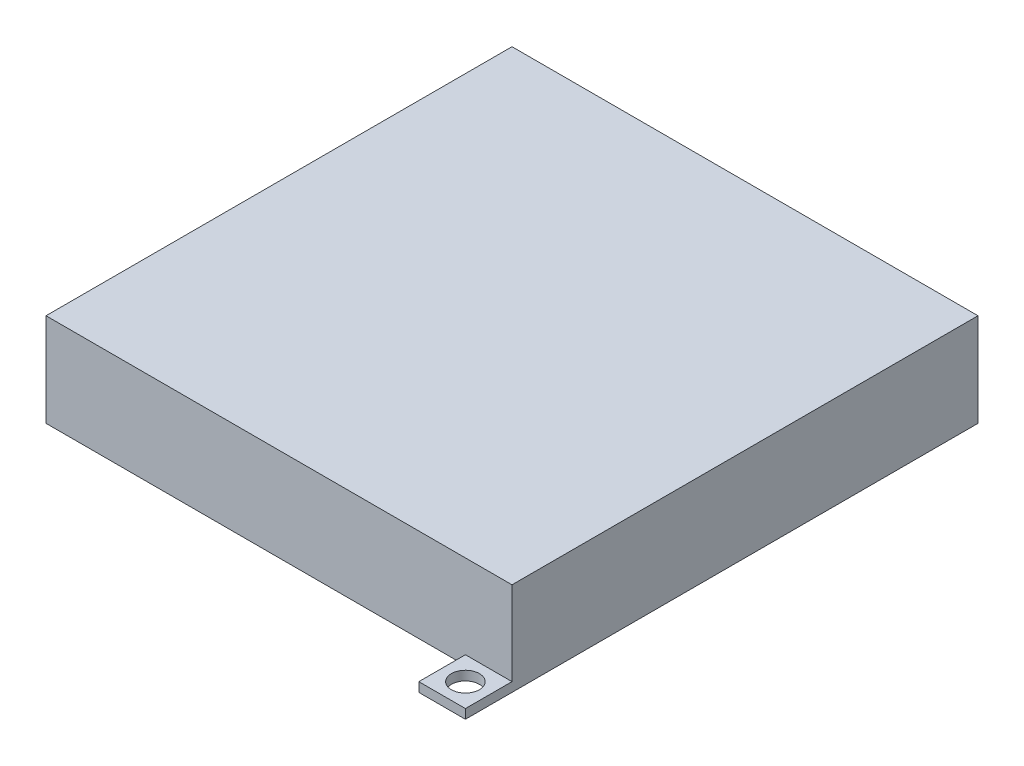
SolidWorks part; units mm, degrees
ref_plane "Front Plane" through (0, 0, 0) normal (0, 0, 1) x (1, 0, 0)
ref_plane "Top Plane" through (0, 0, 0) normal (0, 1, 0) x (1, 0, 0)
ref_plane "Right Plane" through (0, 0, 0) normal (1, 0, 0) x (0, 0, -1)
sketch "Sketch4" plane through (0, 0, 0) normal (0, 1, 0) x (1, 0, 0)
  line L0 (25, -25) -> (-25, -25)
  line L1 (25, -25) -> (25, 25)
  line L2 (-25, -25) -> (-25, 25)
  line L3 (25, 25) -> (-25, 25)
  line L4 (25, -25) -> (-25, 25) construction
  line L5 (-25, -25) -> (25, 25) construction
  point P1 (0, 0)
  dimension "D1" = 50
  dimension "D2" = 50
extrude "Boss-Extrude1" add sketch "Sketch4" along normal blind 10
sketch "Sketch5" plane through (0, 0, 0) normal (0, 1, 0) x (1, 0, 0)
  line L0 (-20, -20) -> (20, -20)
  line L1 (-20, -20) -> (-20, 20)
  line L2 (20, -20) -> (20, 20)
  line L3 (-20, 20) -> (20, 20)
  line L4 (-20, -20) -> (20, 20) construction
  line L5 (20, -20) -> (-20, 20) construction
  point P1 (0, 0)
  dimension "D1" = 40
  dimension "D2" = 40
extrude "Cut-Extrude1" cut sketch "Sketch5" along normal blind 7
sketch "Sketch9" plane through (0, 0, 0) normal (0, -1, 0) x (1, 0, 0)
  line L0 (-25, -25) -> (-25, -30)
  line L1 (-25, -30) -> (-20, -30)
  line L2 (-20, -30) -> (-20, -25)
  line L3 (25, -25) -> (-25, -25) construction
  line L4 (-20, -25) -> (-25, -25)
  line L5 (25, 25) -> (25, 30)
  line L6 (25, 30) -> (20, 30)
  line L7 (20, 30) -> (20, 25)
  line L8 (-25, 25) -> (25, 25) construction
  line L9 (20, 25) -> (25, 25)
  circle A0 centre (22.5, 27.5) radius 1.5
  circle A1 centre (-22.5, -27.5) radius 1.5
  dimension "D5" = 3
  dimension "D6" = 3
  dimension "D1" = 5
  dimension "D2" = 5
  dimension "D3" = 5
  dimension "D4" = 5
extrude "Boss-Extrude4" add sketch "Sketch9" against normal blind 1
